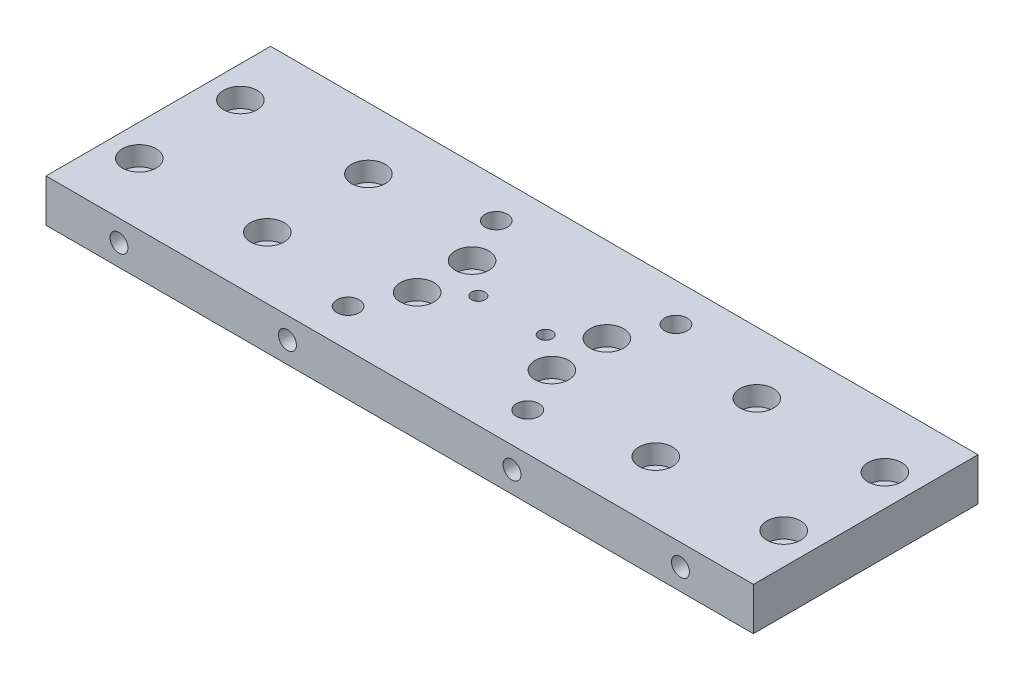
SolidWorks part; units mm, degrees
material "AISI 1020"
ref_plane "Plano frontal" through (0, 0, 0) normal (0, 0, 1) x (1, 0, 0)
ref_plane "Plano superior" through (0, 0, 0) normal (0, 1, 0) x (1, 0, 0)
ref_plane "Plano direito" through (0, 0, 0) normal (1, 0, 0) x (0, 0, -1)
sketch "Esboço1" plane through (0, 0, 0) normal (0, 1, 0) x (1, 0, 0)
  line L1 (-157.5, -50) -> (157.5, -50)
  line L2 (-157.5, -50) -> (-157.5, 50)
  line L3 (-157.5, 50) -> (157.5, 50)
  line L4 (157.5, -50) -> (157.5, 50)
  line L5 (-157.5, -50) -> (157.5, 50) construction
  line L6 (-157.5, 50) -> (157.5, -50) construction
  point P0 (0, 0)
  dimension "D1" = 315
  dimension "D2" = 100
extrude "Ressalto-extrusão1" add sketch "Esboço1" along normal blind 19.02
sketch "Esboço2" plane through (0, 19.02, 0) normal (0, 1, 0) x (1, 0, 0)
  line L0 (157.5, -50) -> (157.5, 50) construction
  circle A0 centre (143.5, 22.5) radius 2
  circle A1 centre (86.5, 22.5) radius 2
  circle A2 centre (86.5, -22.5) radius 2
  circle A3 centre (143.5, -22.5) radius 2
  circle A4 centre (-86.5, -22.45) radius 2
  circle A5 centre (-143.5, -22.45) radius 2
  circle A6 centre (-143.5, 22.55) radius 2
  circle A7 centre (-86.5, 22.55) radius 2
  dimension "D1" = 4
  dimension "D2" = 4
  dimension "D3" = 4
  dimension "D4" = 4
  dimension "D13" = 173
  dimension "D14" = 57
  dimension "D15" = 45
  dimension "D16" = 45
  dimension "D17" = 57
  dimension "D18" = 173
  dimension "D19" = 4
  dimension "D20" = 4
  dimension "D21" = 4
  dimension "D22" = 4
  dimension "D23" = 22.45
  dimension "D24" = 0
  dimension "D5" = 57
  dimension "D6" = 57
  dimension "D7" = 45
  dimension "D8" = 45
  dimension "D9" = 14
  dimension "D10" = 22.5
  dimension "D11" = 22.5
  dimension "D12" = 14
extrude "Corte-extrusão1" cut sketch "Esboço2" against normal blind 25
sketch "Esboço3" plane through (0, 0, 50) normal (0, 0, 1) x (1, 0, 0)
  line L0 (-157.5, 0) -> (157.5, 0) construction
  line L1 (-10, 0) -> (10, 0)
  line L2 (-10, 0) -> (-10, 5)
  line L3 (-10, 5) -> (10, 5)
  line L4 (10, 0) -> (10, 5)
  dimension "D1" = 5
  dimension "D2" = 20
  dimension "D3" = 10
extrude "Corte-extrusão2" [suppressed] cut sketch "Esboço3" against normal through all
sketch "Esboço4" plane through (0, 19.02, 0) normal (0, 1, 0) x (1, 0, 0)
  line L3 (157.5, 50) -> (-157.5, 50) construction
  line L4 (-157.5, -50) -> (157.5, -50) construction
  circle A2 centre (-40, -32.9999) radius 5
  circle A3 centre (-40, 33) radius 5
  circle A4 centre (40, 33) radius 5
  circle A5 centre (40, -33) radius 5
  dimension "D2" = 10
  dimension "D7" = 40
  dimension "D5" = 10
  dimension "D3" = 17
  dimension "D4" = 17
  dimension "D6" = 40
  dimension "D9" = 10
  dimension "D10" = 10
  dimension "D11" = 80
  dimension "D12" = 80
extrude "Corte-extrusão3" cut sketch "Esboço4" against normal through all
sketch "Esboço5" plane through (0, 19.02, 0) normal (0, 1, 0) x (1, 0, 0)
  circle A0 centre (0, 0) radius 3.3
  dimension "D1" = 0
  dimension "D2" = 6.6
extrude "Corte-extrusão4" cut sketch "Esboço5" against normal blind 90
sketch "Esboço6" plane through (0, 19.02, 0) normal (0, 1, 0) x (1, 0, 0)
  circle A0 centre (0, 30) radius 4
  circle A1 centre (0, -30) radius 4
  circle A2 centre (0, 0) radius 3.3 construction
  dimension "D1" = 8
  dimension "D2" = 8
  dimension "D4" = 30
  dimension "D3" = 60
extrude "Corte-extrusão5" [suppressed] cut sketch "Esboço6" against normal through all
sketch "Esboço10" [suppressed] plane through (0, 19.02, 0) normal (0, 1, 0) x (1, 0, 0)
  circle A4 centre (0, 30) radius 7
  circle A5 centre (0, -30) radius 7
extrude "Corte-extrusão7" [suppressed] cut sketch "Esboço10" against normal blind 8
hole_wizard "Rebaixo para parafuso Allen sextavado de M83" positions "3DSketch2" profile "Esboço12" counterbore size "M8" standard "ISO"
sketch3d "3DSketch2"
  line L0 (-143.5, 0, -22.55) -> (-143.5, 19.02, -22.55) construction
  line L1 (-86.5, 0, 22.45) -> (-86.5, 19.02, 22.45) construction
  line L2 (-86.5, 0, -22.55) -> (-86.5, 19.02, -22.55) construction
  line L3 (-143.5, 0, 22.45) -> (-143.5, 19.02, 22.45) construction
  line L4 (86.5, 0, -22.5) -> (86.5, 19.02, -22.5) construction
  line L5 (143.5, 0, -22.5) -> (143.5, 19.02, -22.5) construction
  line L6 (86.5, 0, 22.5) -> (86.5, 19.02, 22.5) construction
  line L7 (143.5, 0, 22.5) -> (143.5, 19.02, 22.5) construction
  point P0 (-143.5, 19.02, -22.55)
  point P4 (-143.17, 0, 22.6988)
  point P6 (-86.5, 19.02, 22.45)
  point P10 (-86.5, 19.02, -22.55)
  point P14 (-143.5, 19.02, 22.45)
  point P18 (86.5, 19.02, -22.5)
  point P22 (143.5, 19.02, -22.5)
  point P26 (86.5, 19.02, 22.5)
  point P30 (143.5, 19.02, 22.5)
sketch "Esboço12" plane through (-143.5, 19.02, -22.55) normal (1, 0, 0) x (0, 0, 1)
  line L0 (0, 0) -> (0, 19.02)
  line L1 (0, 19.02) -> (4.5, 19.02)
  line L3 (4.5, 19.02) -> (4.5, 8.6)
  line L4 (4.5, 8.6) -> (7.5, 8.6)
  line L5 (7.5, 8.6) -> (7.5, 0)
  line L7 (7.5, 0) -> (0, 0)
  line L11 (0, -6.35) -> (0, 107.95) construction
  dimension "Thru Hole Dia." = 9
  dimension "Thru Hole Depth" = 19.02
  dimension "C'Bore Dia." = 15
  dimension "C'Bore Depth" = 8.6
sketch "Esboço13" plane through (0, 0, 50) normal (0, 0, 1) x (1, 0, 0)
  line L0 (-157.5, 19.02) -> (157.5, 19.02) construction
  circle A0 centre (-125, 9.51) radius 4
  circle A1 centre (-50, 9.51) radius 4
  circle A2 centre (50, 9.51) radius 4
  circle A3 centre (125, 9.51) radius 4
  dimension "D1" = 100
  dimension "D2" = 250
  dimension "D3" = 75
  dimension "D5" = 9.51
  dimension "D6" = 9.51
  dimension "D4" = 50
extrude "Corte-extrusão8" cut sketch "Esboço13" against normal blind 20
cosmetic thread "Representação de rosca1" parameters "D2"=10
cosmetic thread "Representação de rosca2" parameters "D2"=10
cosmetic thread "Representação de rosca3" parameters "D2"=10
cosmetic thread "Representação de rosca4" parameters "D2"=10
sketch "Esboço14" plane through (0, 0, -50) normal (0, 0, -1) x (-1, 0, 0)
  line L0 (-157.5, 19.02) -> (157.5, 19.02) construction
  circle A0 centre (-125, 9.51) radius 4
  circle A1 centre (-50, 9.51) radius 4
  circle A2 centre (50, 9.51) radius 4
  circle A3 centre (125, 9.51) radius 4
  dimension "D1" = 9.51
  dimension "D2" = 9.51
  dimension "D3" = 9.51
  dimension "D4" = 9.51
  dimension "D5" = 250
  dimension "D6" = 100
  dimension "D7" = 75
  dimension "D8" = 50
  dimension "D9" = 8
  dimension "D10" = 8
  dimension "D11" = 8
  dimension "D12" = 8
extrude "Corte-extrusão9" cut sketch "Esboço14" against normal blind 20
cosmetic thread "Representação de rosca5" parameters "D2"=10
cosmetic thread "Representação de rosca6" parameters "D2"=10
cosmetic thread "Representação de rosca7" parameters "D2"=10
cosmetic thread "Representação de rosca8" parameters "D2"=10
sketch "Esboço15" plane through (0, 19.02, 0) normal (0, 1, 0) x (1, 0, 0)
  circle A0 centre (30, 12.225) radius 4
  circle A1 centre (30, -12.225) radius 4
  circle A2 centre (-30, 12.225) radius 4
  circle A3 centre (-30, -12.225) radius 4
  circle A4 centre (0, 0) radius 3.3 construction
  circle A5 centre (-15, 0) radius 3
  circle A6 centre (15, 0) radius 3
  dimension "D1" = 8
  dimension "D2" = 8
  dimension "D3" = 8
  dimension "D4" = 8
  dimension "D5" = 30
  dimension "D6" = 30
  dimension "D7" = 30
  dimension "D8" = 30
  dimension "D9" = 15
  dimension "D10" = 15
  dimension "D11" = 24.45
  dimension "D12" = 24.45
  dimension "D13" = 12.225
  dimension "D14" = 12.225
extrude "Corte-extrusão10" cut sketch "Esboço15" against normal through all
sketch "Esboço16" plane through (0, 19.02, 0) normal (0, 1, 0) x (1, 0, 0)
  circle A0 centre (0, 0) radius 3.3
extrude "Ressalto-extrusão2" add sketch "Esboço16" along direction (0, -1, 0) on the side against the normal up to surface (19.02 mm away)
thread "Rosca1" [suppressed] pitch 1.25 start angle 0, offset 0, length 0, pitch 1.25, diameter 8
ref_plane "Plano1" through (129, 9.51, -50) normal (0, -1, 0) x (1, 0, 0)
sketch "Perfil da rosca1" plane through (129, 9.51, -50) normal (0, -1, 0) x (1, 0, 0)
  line L0 (0, 0) -> (0, 1.25) construction
  line L11 (0, 0) -> (0, 1.0937)
  line L12 (0, 1.0937) -> (-0.6766, 0.7031)
  line L13 (-0.6766, 0.7031) -> (-0.6766, 0.3906)
  line L15 (-0.6766, 0.3906) -> (0, 0)
  line L17 (-0.6766, 0.5469) -> (0, 0.5469) construction
  point P2 (0, 0)
  dimension "Pitch" = 1.25
  dimension "Profile_Angle" = 60
  dimension "Profile_Land" = 0.3125
  dimension "Profile_Height" = 0.6766
thread "Rosca2" [suppressed] pitch 1.25 start angle 0, offset 0, length 0, pitch 1.25, diameter 8
ref_plane "Plano2" through (54, 9.51, -50) normal (0, -1, 0) x (1, 0, 0)
sketch "Perfil da rosca2" plane through (54, 9.51, -50) normal (0, -1, 0) x (1, 0, 0)
  line L0 (0, 0) -> (0, 1.25) construction
  line L11 (0, 0) -> (0, 1.0937)
  line L12 (0, 1.0937) -> (-0.6766, 0.7031)
  line L13 (-0.6766, 0.7031) -> (-0.6766, 0.3906)
  line L15 (-0.6766, 0.3906) -> (0, 0)
  line L17 (-0.6766, 0.5469) -> (0, 0.5469) construction
  point P2 (0, 0)
  dimension "Pitch" = 1.25
  dimension "Profile_Angle" = 60
  dimension "Profile_Land" = 0.3125
  dimension "Profile_Height" = 0.6766
thread "Rosca3" [suppressed] pitch 1.25 start angle 0, offset 0, length 0, pitch 1.25, diameter 8
ref_plane "Plano3" through (-46, 9.51, -50) normal (0, -1, 0) x (1, 0, 0)
sketch "Perfil da rosca3" plane through (-46, 9.51, -50) normal (0, -1, 0) x (1, 0, 0)
  line L0 (0, 0) -> (0, 1.25) construction
  line L11 (0, 0) -> (0, 1.0937)
  line L12 (0, 1.0937) -> (-0.6766, 0.7031)
  line L13 (-0.6766, 0.7031) -> (-0.6766, 0.3906)
  line L15 (-0.6766, 0.3906) -> (0, 0)
  line L17 (-0.6766, 0.5469) -> (0, 0.5469) construction
  point P2 (0, 0)
  dimension "Pitch" = 1.25
  dimension "Profile_Angle" = 60
  dimension "Profile_Land" = 0.3125
  dimension "Profile_Height" = 0.6766
thread "Rosca4" [suppressed] pitch 1.25 start angle 0, offset 0, length 0, pitch 1.25, diameter 8
ref_plane "Plano4" through (-121, 9.51, -50) normal (0, -1, 0) x (1, 0, 0)
sketch "Perfil da rosca4" plane through (-121, 9.51, -50) normal (0, -1, 0) x (1, 0, 0)
  line L0 (0, 0) -> (0, 1.25) construction
  line L11 (0, 0) -> (0, 1.0937)
  line L12 (0, 1.0937) -> (-0.6766, 0.7031)
  line L13 (-0.6766, 0.7031) -> (-0.6766, 0.3906)
  line L15 (-0.6766, 0.3906) -> (0, 0)
  line L17 (-0.6766, 0.5469) -> (0, 0.5469) construction
  point P2 (0, 0)
  dimension "Pitch" = 1.25
  dimension "Profile_Angle" = 60
  dimension "Profile_Land" = 0.3125
  dimension "Profile_Height" = 0.6766
thread "Rosca5" [suppressed] pitch 1.25 start angle 0, offset 0, length 0, pitch 1.25, diameter 8
ref_plane "Plano5" through (-129, 9.51, 50) normal (0, -1, 0) x (-1, 0, 0)
sketch "Perfil da rosca5" plane through (-129, 9.51, 50) normal (0, -1, 0) x (-1, 0, 0)
  line L0 (0, 0) -> (0, 1.25) construction
  line L11 (0, 0) -> (0, 1.0937)
  line L12 (0, 1.0937) -> (-0.6766, 0.7031)
  line L13 (-0.6766, 0.7031) -> (-0.6766, 0.3906)
  line L15 (-0.6766, 0.3906) -> (0, 0)
  line L17 (-0.6766, 0.5469) -> (0, 0.5469) construction
  point P2 (0, 0)
  dimension "Pitch" = 1.25
  dimension "Profile_Angle" = 60
  dimension "Profile_Land" = 0.3125
  dimension "Profile_Height" = 0.6766
thread "Rosca6" [suppressed] pitch 1.25 start angle 0, offset 0, length 0, pitch 1.25, diameter 8
ref_plane "Plano6" through (-54, 9.51, 50) normal (0, -1, 0) x (-1, 0, 0)
sketch "Perfil da rosca6" plane through (-54, 9.51, 50) normal (0, -1, 0) x (-1, 0, 0)
  line L0 (0, 0) -> (0, 1.25) construction
  line L11 (0, 0) -> (0, 1.0937)
  line L12 (0, 1.0937) -> (-0.6766, 0.7031)
  line L13 (-0.6766, 0.7031) -> (-0.6766, 0.3906)
  line L15 (-0.6766, 0.3906) -> (0, 0)
  line L17 (-0.6766, 0.5469) -> (0, 0.5469) construction
  point P2 (0, 0)
  dimension "Pitch" = 1.25
  dimension "Profile_Angle" = 60
  dimension "Profile_Land" = 0.3125
  dimension "Profile_Height" = 0.6766
thread "Rosca7" [suppressed] pitch 1.25 start angle 0, offset 0, length 0, pitch 1.25, diameter 8
ref_plane "Plano7" through (46, 9.51, 50) normal (0, -1, 0) x (-1, 0, 0)
sketch "Perfil da rosca7" plane through (46, 9.51, 50) normal (0, -1, 0) x (-1, 0, 0)
  line L0 (0, 0) -> (0, 1.25) construction
  line L11 (0, 0) -> (0, 1.0937)
  line L12 (0, 1.0937) -> (-0.6766, 0.7031)
  line L13 (-0.6766, 0.7031) -> (-0.6766, 0.3906)
  line L15 (-0.6766, 0.3906) -> (0, 0)
  line L17 (-0.6766, 0.5469) -> (0, 0.5469) construction
  point P2 (0, 0)
  dimension "Pitch" = 1.25
  dimension "Profile_Angle" = 60
  dimension "Profile_Land" = 0.3125
  dimension "Profile_Height" = 0.6766
thread "Rosca8" [suppressed] pitch 1.25 start angle 0, offset 0, length 0, pitch 1.25, diameter 8
ref_plane "Plano8" through (121, 9.51, 50) normal (0, -1, 0) x (-1, 0, 0)
sketch "Perfil da rosca8" plane through (121, 9.51, 50) normal (0, -1, 0) x (-1, 0, 0)
  line L0 (0, 0) -> (0, 1.25) construction
  line L11 (0, 0) -> (0, 1.0937)
  line L12 (0, 1.0937) -> (-0.6766, 0.7031)
  line L13 (-0.6766, 0.7031) -> (-0.6766, 0.3906)
  line L15 (-0.6766, 0.3906) -> (0, 0)
  line L17 (-0.6766, 0.5469) -> (0, 0.5469) construction
  point P2 (0, 0)
  dimension "Pitch" = 1.25
  dimension "Profile_Angle" = 60
  dimension "Profile_Land" = 0.3125
  dimension "Profile_Height" = 0.6766
hole_wizard "Rebaixo para parafuso Allen sextavado de M82" positions "3DSketch4" profile "Esboço34" counterbore size "M8" standard "ISO" end condition through all
sketch3d "3DSketch4"
  line L0 (-30, 0, -12.225) -> (-30, 19.02, -12.225) construction
  line L1 (30, 0, -12.225) -> (30, 19.02, -12.225) construction
  line L2 (30, 0, 12.225) -> (30, 19.02, 12.225) construction
  line L3 (-30, 0, 12.225) -> (-30, 19.02, 12.225) construction
  point P0 (-30, 19.02, -12.225)
  point P4 (30, 19.02, -12.225)
  point P8 (30, 19.02, 12.225)
  point P12 (-30, 19.02, 12.225)
sketch "Esboço34" plane through (-30, 19.02, -12.225) normal (1, 0, 0) x (0, 0, 1)
  line L0 (0, 0) -> (0, 19.02)
  line L1 (0, 19.02) -> (4.5, 19.02)
  line L3 (4.5, 19.02) -> (4.5, 8.6)
  line L4 (4.5, 8.6) -> (7.5, 8.6)
  line L5 (7.5, 8.6) -> (7.5, 0)
  line L7 (7.5, 0) -> (0, 0)
  line L11 (0, -6.35) -> (0, 107.95) construction
  dimension "Thru Hole Dia." = 9
  dimension "Thru Hole Depth" = 19.02
  dimension "C'Bore Dia." = 15
  dimension "C'Bore Depth" = 8.6
